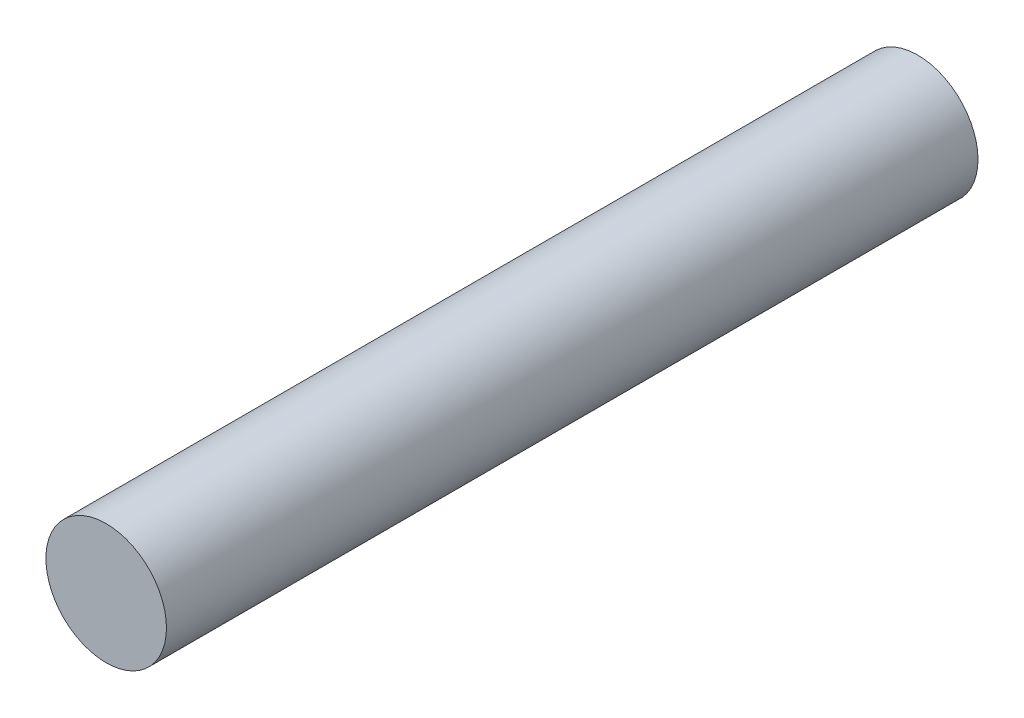
SolidWorks part; units mm, degrees
ref_plane "Front Plane" through (0, 0, 0) normal (0, 0, 1) x (1, 0, 0)
ref_plane "Top Plane" through (0, 0, 0) normal (0, 1, 0) x (1, 0, 0)
ref_plane "Right Plane" through (0, 0, 0) normal (1, 0, 0) x (0, 0, -1)
sketch "Sketch1" plane through (0, 0, 0) normal (0, 0, 1) x (1, 0, 0)
  circle A0 centre (0, 0) radius 3.302
  dimension "D1" = 6.604
extrude "Extrude1" add sketch "Sketch1" along normal blind 44.45
